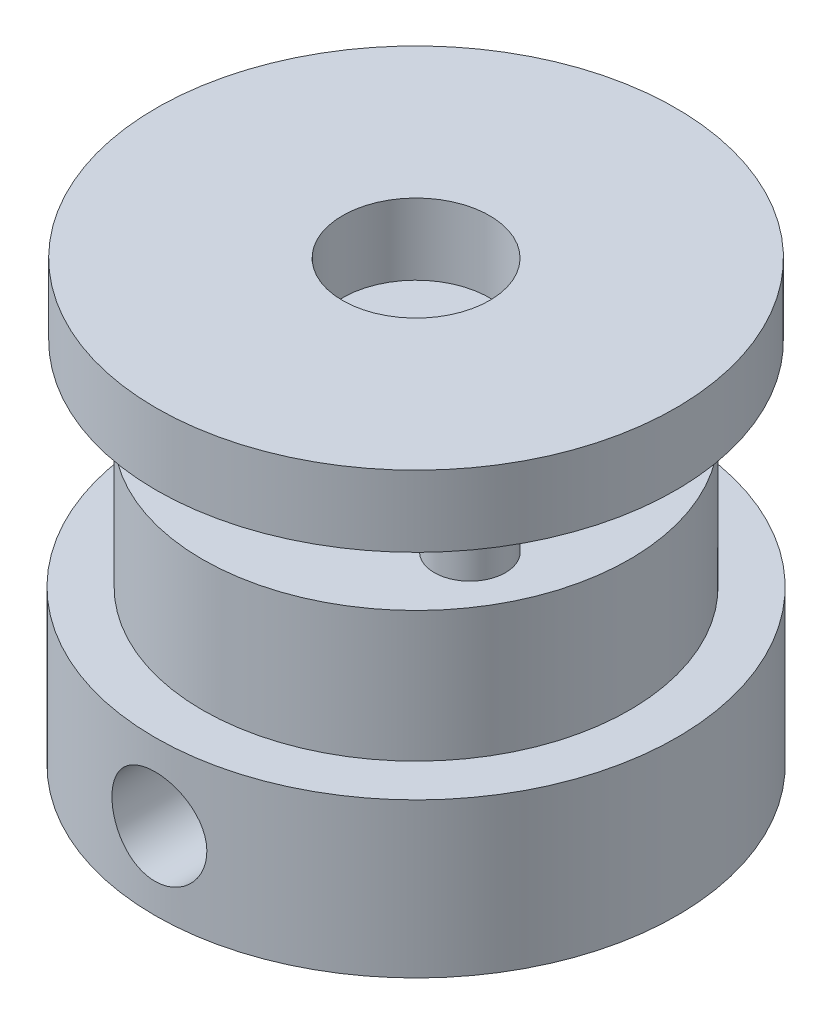
SolidWorks part; units mm, degrees
material "1060 Alloy"
ref_plane "Front Plane" through (0, 0, 0) normal (0, 0, 1) x (1, 0, 0)
ref_plane "Top Plane" through (0, 0, 0) normal (0, 1, 0) x (1, 0, 0)
ref_plane "Right Plane" through (0, 0, 0) normal (1, 0, 0) x (0, 0, -1)
sketch "Sketch1" plane through (0, 0, 0) normal (0, 1, 0) x (1, 0, 0)
  circle A0 centre (0, 0) radius 11
  dimension "D1" = 22
extrude "Boss-Extrude1" add sketch "Sketch1" along normal blind 6.5
sketch "Sketch2" plane through (0, 6.5, 0) normal (0, 1, 0) x (1, 0, 0)
  circle A0 centre (0, 0) radius 9
  dimension "D1" = 18
extrude "Boss-Extrude2" add sketch "Sketch2" along normal blind 5.5
sketch "Sketch3" plane through (0, 12, 0) normal (0, 1, 0) x (1, 0, 0)
  circle A0 centre (0, 0) radius 3
  dimension "D1" = 6
extrude "Cut-Extrude1" cut sketch "Sketch3" against normal through all
sketch "Sketch4" plane through (0, 12, 0) normal (0, 1, 0) x (1, 0, 0)
  circle A0 centre (0, 6.2) radius 1.5
  dimension "D1" = 3
  dimension "D2" = 6.2
extrude "Boss-Extrude3" add sketch "Sketch4" along normal blind 3.5
pattern_circular "CirPattern1" count 3 over 360 about axis through (0, 0, 0) along (0, 1, 0) of "Boss-Extrude3"
sketch "Sketch5" plane through (0, 15.5, 0) normal (0, 1, 0) x (1, 0, 0)
  circle A0 centre (0, 0) radius 10.95
  circle A1 centre (0, 0) radius 3.1
  dimension "D1" = 21.9
  dimension "D2" = 6.2
extrude "Boss-Extrude4" add sketch "Sketch5" along normal blind 3
sketch "Sketch7" plane through (0, 0, 0) normal (0, 0, 1) x (1, 0, 0)
  circle A0 centre (0, 3.25) radius 2
  dimension "D2" = 4
  dimension "D1" = 3.25
extrude "Cut-Extrude2" cut sketch "Sketch7" along normal through all
